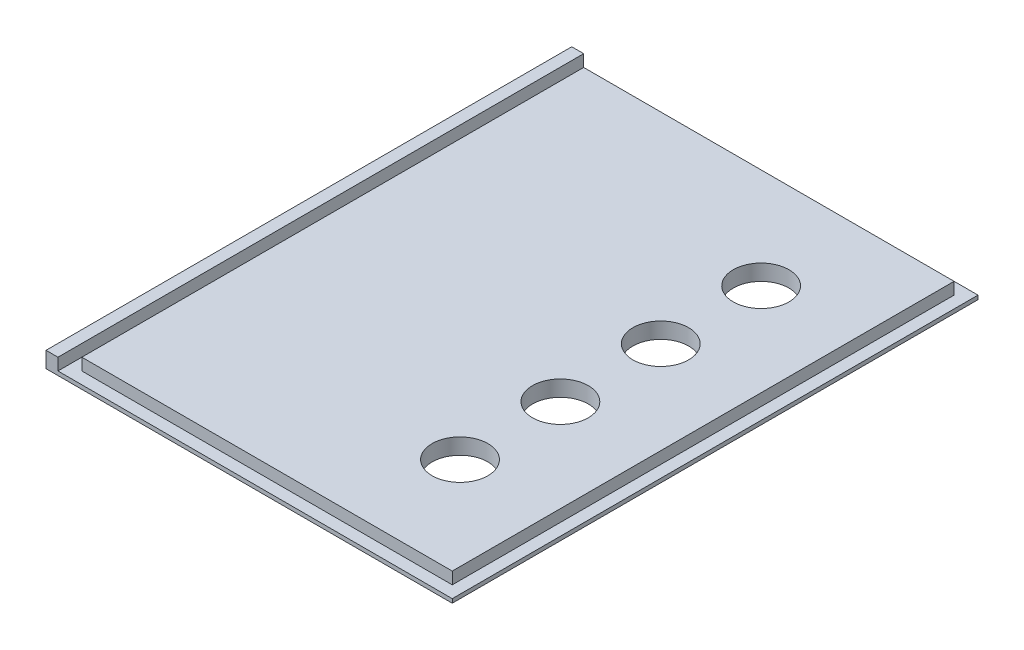
SolidWorks part; units mm, degrees
ref_plane "Front Plane" through (0, 0, 0) normal (0, 0, 1) x (1, 0, 0)
ref_plane "Top Plane" through (0, 0, 0) normal (0, 1, 0) x (1, 0, 0)
ref_plane "Right Plane" through (0, 0, 0) normal (1, 0, 0) x (0, 0, -1)
sketch "Sketch1" plane through (0, 0, 0) normal (0, 1, 0) x (1, 0, 0)
  line L1 (-51, 66) -> (51, 66)
  line L2 (-51, 66) -> (-51, -66)
  line L3 (-51, -66) -> (51, -66)
  line L4 (51, 66) -> (51, -66)
  line L5 (-51, 66) -> (51, -66) construction
  line L6 (-51, -66) -> (51, 66) construction
  point P0 (0, 0)
  dimension "D1" = 132
  dimension "D2" = 102
extrude "Boss-Extrude2" add sketch "Sketch1" along normal blind 1
sketch "Sketch2" plane through (0, 1, 0) normal (0, 1, 0) x (1, 0, 0)
  line L18 (-51, -66) -> (51, -66) construction
  line L23 (-51, 66) -> (-48, 66)
  line L24 (-51, 66) -> (-51, -66)
  line L25 (-51, -66) -> (-48, -66)
  line L26 (-48, 66) -> (-48, -66)
  dimension "D1" = 3
extrude "Boss-Extrude5" add sketch "Sketch2" along normal blind 3
sketch "Sketch3" plane through (0, 1, 0) normal (0, 1, 0) x (1, 0, 0)
  line L0 (51, 66) -> (-48, 66) construction
  line L1 (-45, 63) -> (48, 63)
  line L2 (-45, 63) -> (-45, -63)
  line L3 (-45, -63) -> (48, -63)
  line L4 (48, 63) -> (48, -63)
  line L5 (-45, 63) -> (48, -63) construction
  line L6 (-45, -63) -> (48, 63) construction
  line L7 (-48, -66) -> (-48, 66) construction
  point P0 (1.5, 0)
  dimension "D1" = 93
  dimension "D2" = 126
  dimension "D3" = 3
  dimension "D4" = 3
extrude "Boss-Extrude6" add sketch "Sketch3" along normal blind 3
sketch "Sketch4" plane through (0, 0, 0) normal (0, 1, 0) x (1, 0, 0)
  line L0 (1.5, 63) -> (48, 63) construction
  line L1 (48, 63) -> (-45, 63) construction
  line L2 (48, 63) -> (-45, 63) construction
  line L3 (-45, -63) -> (48, -63) construction
  circle A0 centre (24.75, 12.6) radius 7
  circle A1 centre (24.75, -12.6) radius 7
  circle A2 centre (24.75, 37.8) radius 7
  circle A3 centre (24.75, -37.8) radius 7
  point P17 (24.75, 63)
  dimension "D5" = 14
  dimension "D3" = 25.2
  dimension "D1" = 25.2
  dimension "D2" = 25.2
  dimension "D4" = 25.2
  dimension "D6" = 25.2
extrude "Cut-Extrude1" cut sketch "Sketch4" along normal up to surface (4 mm away) up to face at (1.5, 4, 0)
